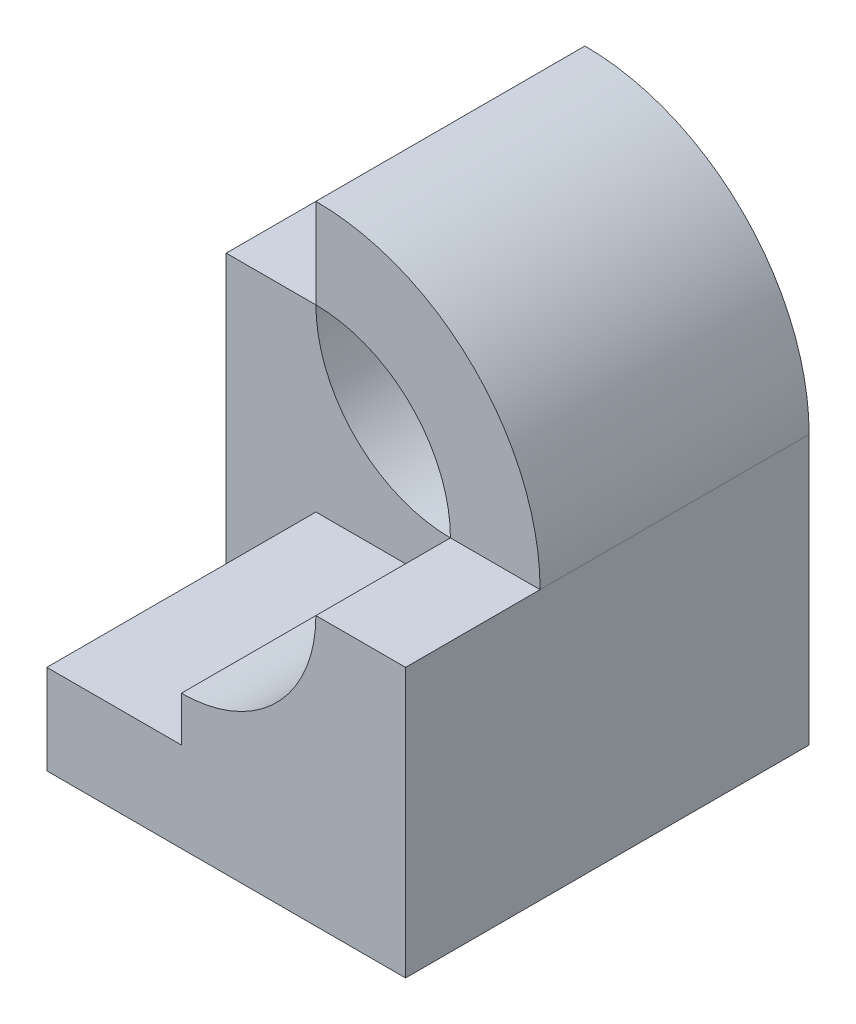
SolidWorks part; units mm, degrees
ref_plane "Front" through (0, 0, 0) normal (0, 0, 1) x (1, 0, 0)
ref_plane "Top" through (0, 0, 0) normal (0, 1, 0) x (1, 0, 0)
ref_plane "Right" through (0, 0, 0) normal (1, 0, 0) x (0, 0, -1)
sketch "Sketch1" plane through (0, 0, 0) normal (0, 0, 1) x (1, 0, 0)
  line L0 (5, 11) -> (5, 9)
  line L1 (0, 0) -> (10, 0)
  line L2 (0, 0) -> (0, 6)
  line L3 (0, 6) -> (2, 6)
  line L4 (10, 0) -> (10, 6)
  circle A0 centre (5, 6) radius 3
  arc A1 (10, 6) -> (5, 11) centre (5, 6) ccw
  dimension "D3" = 6
  dimension "D4" = 5
  dimension "D1" = 6
  dimension "D2" = 10
  dimension "D5" = 5
  dimension "D6" = 5
extrude "Boss-Extrude1" add sketch "Sketch1" along normal blind 9 contours L4 A1 L0 A0 L3 L2 L1
sketch "Sketch2" plane through (0, 0, 9) normal (0, 0, 1) x (1, 0, 0)
  line L1 (5, 11) -> (10, 11)
  line L2 (5, 11) -> (5, 6)
  line L3 (5, 6) -> (10, 6)
  line L4 (10, 11) -> (10, 6)
extrude "Cut-Extrude1" cut sketch "Sketch2" against normal blind 3
sketch "Sketch3" plane through (0, 0, 9) normal (0, 0, 1) x (1, 0, 0)
  line L0 (5, 3) -> (5, 2)
  line L1 (5, 2) -> (2, 2)
  line L2 (2, 2) -> (2, 0)
  line L3 (0, 0) -> (10, 0) construction
  line L4 (2, 0) -> (0, 0)
  line L5 (0, 0) -> (0, 6.616)
  line L6 (0, 6.616) -> (4.6545, 5.7143)
  line L7 (4.6545, 5.7143) -> (5, 3)
  arc A0 (2, 6) -> (8, 6) centre (5, 6) ccw construction
  dimension "D1" = 1
  dimension "D2" = 3
extrude "Cut-Extrude2" cut sketch "Sketch3" against normal blind 6
